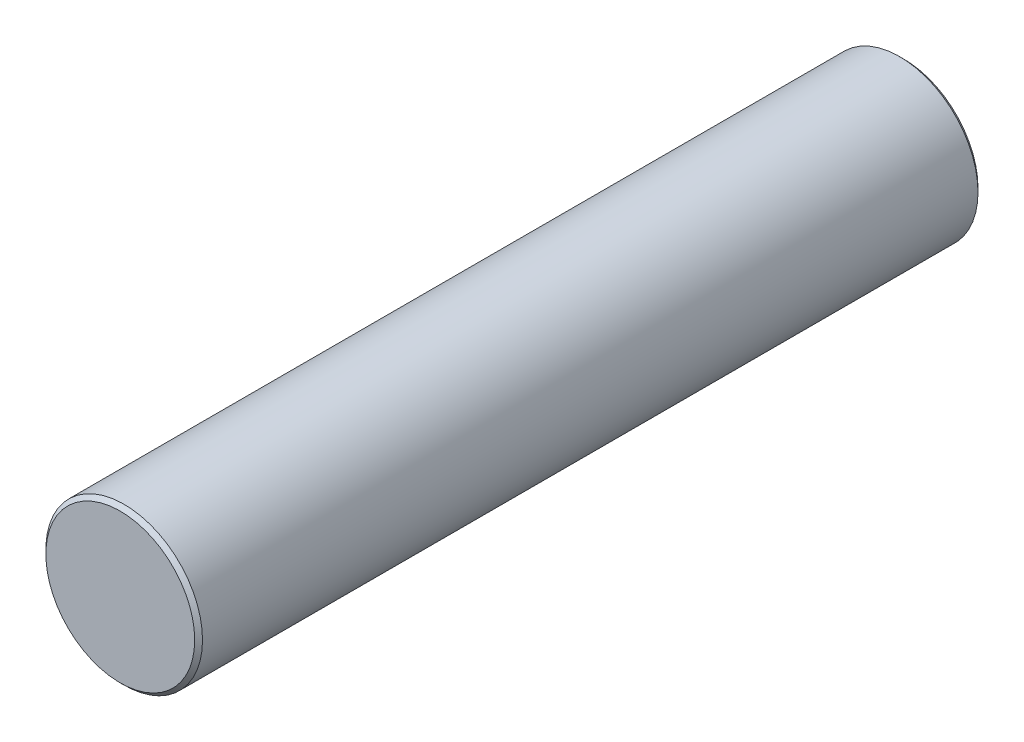
SolidWorks part; units mm, degrees
material "Cast Alloy Steel"
ref_plane "Front Plane" through (0, 0, 0) normal (0, 0, 1) x (1, 0, 0)
ref_plane "Top Plane" through (0, 0, 0) normal (0, 1, 0) x (1, 0, 0)
ref_plane "Right Plane" through (0, 0, 0) normal (1, 0, 0) x (0, 0, -1)
sketch "Sketch1" plane through (0, 0, 0) normal (0, 0, 1) x (1, 0, 0)
  circle A0 centre (0, 0) radius 20
  dimension "D1" = 40
extrude "Boss-Extrude1" add sketch "Sketch1" along normal blind 200
chamfer "Chamfer1" distance 1 angle 45 2 edges at (20, 0, 0) (20, 0, 200)
